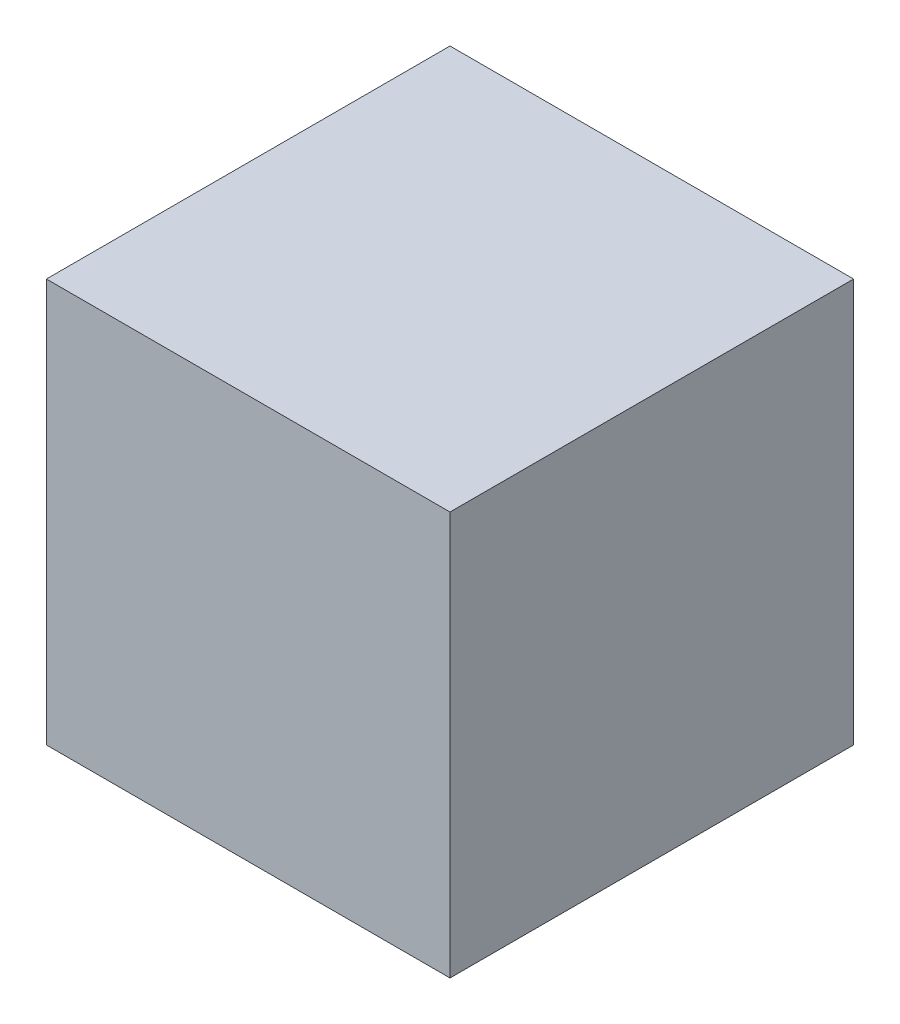
SolidWorks part; units mm, degrees
ref_plane "Front Plane" through (0, 0, 0) normal (0, 0, 1) x (1, 0, 0)
ref_plane "Top Plane" through (0, 0, 0) normal (0, 1, 0) x (1, 0, 0)
ref_plane "Right Plane" through (0, 0, 0) normal (1, 0, 0) x (0, 0, -1)
sketch "Sketch1" plane through (0, 0, 0) normal (0, 1, 0) x (1, 0, 0)
  line L1 (-25.4, -25.4) -> (25.4, -25.4)
  line L2 (-25.4, -25.4) -> (-25.4, 25.4)
  line L3 (-25.4, 25.4) -> (25.4, 25.4)
  line L4 (25.4, -25.4) -> (25.4, 25.4)
  line L5 (-25.4, -25.4) -> (25.4, 25.4) construction
  line L6 (-25.4, 25.4) -> (25.4, -25.4) construction
  point P0 (0, 0)
  dimension "D1" = 50.8
  dimension "D2" = 50.8
extrude "Boss-Extrude1" add sketch "Sketch1" along normal blind 50.8
